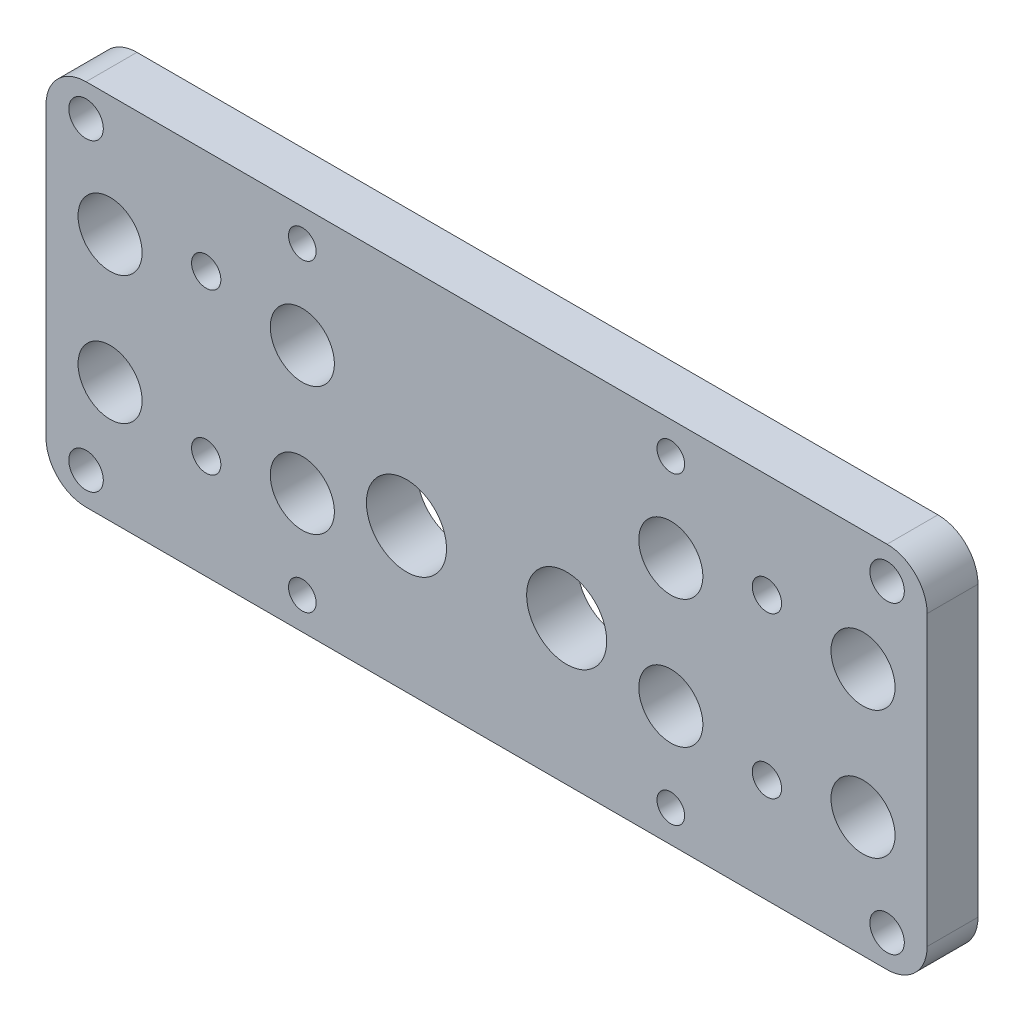
SolidWorks part; units mm, degrees
ref_plane "Front Plane" through (0, 0, 0) normal (0, 0, 1) x (1, 0, 0)
ref_plane "Top Plane" through (0, 0, 0) normal (0, 1, 0) x (1, 0, 0)
ref_plane "Right Plane" through (0, 0, 0) normal (1, 0, 0) x (0, 0, -1)
sketch "Sketch1" plane through (0, 0, 0) normal (0, 0, 1) x (1, 0, 0)
  line L0 (-55, -23) -> (-55, 23)
  line L1 (-55, -23) -> (55, -23)
  line L2 (-55, 23) -> (55, 23)
  line L3 (55, -23) -> (55, 23)
  line L4 (-55, -23) -> (55, 23) construction
  line L5 (-55, 23) -> (55, -23) construction
  point P1 (0, 0)
  dimension "D1" = 110
  dimension "D2" = 46
extrude "Boss-Extrude1" add sketch "Sketch1" along normal blind 6.35
sketch "Sketch2" plane through (0, 0, 0) normal (0, 0, -1) x (-1, 0, 0)
  line L0 (-35, -10) -> (-35, 10) construction
  line L1 (-35, -10) -> (35, -10) construction
  line L2 (-35, 10) -> (35, 10) construction
  line L3 (35, -10) -> (35, 10) construction
  line L4 (-35, -10) -> (35, 10) construction
  line L5 (-35, 10) -> (35, -10) construction
  point P1 (0, 0)
  dimension "D1" = 70
  dimension "D2" = 20
sketch "Sketch5" plane through (0, 0, 0) normal (0, 0, -1) x (-1, 0, 0)
  line L0 (-10, -5) -> (10, -5) construction
  circle A0 centre (-10, -5) radius 5
  circle A1 centre (10, -5) radius 5
  point P4 (0, -5)
  dimension "D2" = 10
  dimension "D3" = 10
  dimension "D1" = 20
  dimension "D4" = 5
extrude "Cut-Extrude1" cut sketch "Sketch5" against normal through all
sketch "Sketch7" plane through (0, 0, 0) normal (0, 0, -1) x (-1, 0, 0)
  line L1 (-23, -8) -> (23, -8) construction
  line L2 (-23, -8) -> (-23, 8) construction
  line L3 (-23, 8) -> (23, 8) construction
  line L4 (23, -8) -> (23, 8) construction
  line L5 (-23, -8) -> (23, 8) construction
  line L6 (-23, 8) -> (23, -8) construction
  line L7 (-47, -8) -> (-23, -8) construction
  line L8 (-47, -8) -> (-47, 8) construction
  line L9 (-47, 8) -> (-23, 8) construction
  line L10 (-23, -8) -> (-23, 8) construction
  line L11 (-47, -8) -> (-23, 8) construction
  line L12 (-47, 8) -> (-23, -8) construction
  line L13 (23, -8) -> (47, -8) construction
  line L14 (23, -8) -> (23, 8) construction
  line L15 (23, 8) -> (47, 8) construction
  line L16 (47, -8) -> (47, 8) construction
  line L17 (23, -8) -> (47, 8) construction
  line L18 (23, 8) -> (47, -8) construction
  circle A0 centre (-23, 8) radius 4
  circle A1 centre (-23, -8) radius 4
  circle A2 centre (23, -8) radius 4
  circle A3 centre (23, 8) radius 4
  circle A4 centre (-47, 8) radius 4
  circle A5 centre (-47, -8) radius 4
  circle A6 centre (47, 8) radius 4
  circle A7 centre (47, -8) radius 4
  point P0 (0, 0)
  point P10 (-35, 0)
  point P15 (35, 0)
  dimension "D3" = 8
  dimension "D1" = 46
  dimension "D2" = 16
  dimension "D4" = 24
  dimension "D5" = 24
extrude "Cut-Extrude2" cut sketch "Sketch7" against normal through all
sketch "Sketch8" plane through (0, 0, 0) normal (0, 0, -1) x (-1, 0, 0)
  line L1 (-23, -19) -> (23, -19) construction
  line L2 (-23, -19) -> (-23, 19) construction
  line L3 (-23, 19) -> (23, 19) construction
  line L4 (23, -19) -> (23, 19) construction
  line L5 (-23, -19) -> (23, 19) construction
  line L6 (-23, 19) -> (23, -19) construction
  line L7 (-50, -19) -> (50, -19) construction
  line L8 (-50, -19) -> (-50, 19) construction
  line L9 (-50, 19) -> (50, 19) construction
  line L10 (50, -19) -> (50, 19) construction
  line L11 (-50, -19) -> (50, 19) construction
  line L12 (-50, 19) -> (50, -19) construction
  point P0 (0, 0)
  point P6 (0, 0)
  dimension "D1" = 38
  dimension "D2" = 46
  dimension "D3" = 38
  dimension "D4" = 100
fillet "Fillet1" radius 5 4 edges at (-55, 23, 3.175) (-55, -23, 3.175) (55, -23, 3.175) (55, 23, 3.175)
hole_wizard "#8-32 Tapped Hole1" positions "Sketch10" profile "Sketch9" tap size "#8-32" standard "ANSI Inch" end condition through all
sketch "Sketch10" plane through (0, 0, 0) normal (0, 0, -1) x (-1, 0, 0)
  point P0 (-23, 19)
  point P3 (23, 19)
  point P6 (23, -19)
  point P9 (-23, -19)
sketch "Sketch9" plane through (23, 19, 0) normal (1, 0, 0) x (0, 1, 0)
  line L0 (0, 0) -> (0, 6.35)
  line L1 (0, 6.35) -> (1.7272, 6.35)
  line L2 (1.7272, 6.35) -> (1.7272, 0)
  line L5 (1.7272, 0) -> (0, 0)
  line L11 (0, -6.35) -> (0, 107.95) construction
  dimension "Thru Tap Drill Dia." = 3.4544
  dimension "Thru Tap Drill Depth" = 6.35
cosmetic thread "Hole Thread1" parameters "D2"=4.1656
cosmetic thread "Hole Thread2" parameters "D2"=4.1656
cosmetic thread "Hole Thread3" parameters "D2"=4.1656
cosmetic thread "Hole Thread4" parameters "D2"=4.1656
hole_wizard "#8 Clearance Hole1" positions "Sketch12" profile "Sketch11" hole size "#8" standard "ANSI Inch" end condition through all
sketch "Sketch12" plane through (0, 0, 0) normal (0, 0, -1) x (-1, 0, 0)
  point P0 (-50, 19)
  point P3 (-50, -19)
  point P6 (50, -19)
  point P9 (50, 19)
sketch "Sketch11" plane through (50, 19, 0) normal (1, 0, 0) x (0, 1, 0)
  line L0 (0, 0) -> (0, 6.35)
  line L1 (0, 6.35) -> (2.1526, 6.35)
  line L2 (2.1526, 6.35) -> (2.1526, 0)
  line L5 (2.1526, 0) -> (0, 0)
  line L11 (0, -6.35) -> (0, 107.95) construction
  dimension "Thru Hole Dia." = 4.3053
  dimension "Thru Hole Depth" = 6.35
hole_wizard "#6 Clearance Hole2" positions "Sketch15" profile "Sketch16" hole size "#6" standard "ANSI Inch" end condition through all
sketch "Sketch15" plane through (0, 0, 0) normal (0, 0, -1) x (-1, 0, 0)
  point P0 (-35, 10)
  point P3 (-35, -10)
  point P6 (35, -10)
  point P9 (35, 10)
sketch "Sketch16" plane through (35, 10, 0) normal (1, 0, 0) x (0, 1, 0)
  line L0 (0, 0) -> (0, 6.35)
  line L1 (0, 6.35) -> (1.8288, 6.35)
  line L2 (1.8288, 6.35) -> (1.8288, 0)
  line L5 (1.8288, 0) -> (0, 0)
  line L11 (0, -6.35) -> (0, 107.95) construction
  dimension "Thru Hole Dia." = 3.6576
  dimension "Thru Hole Depth" = 6.35
